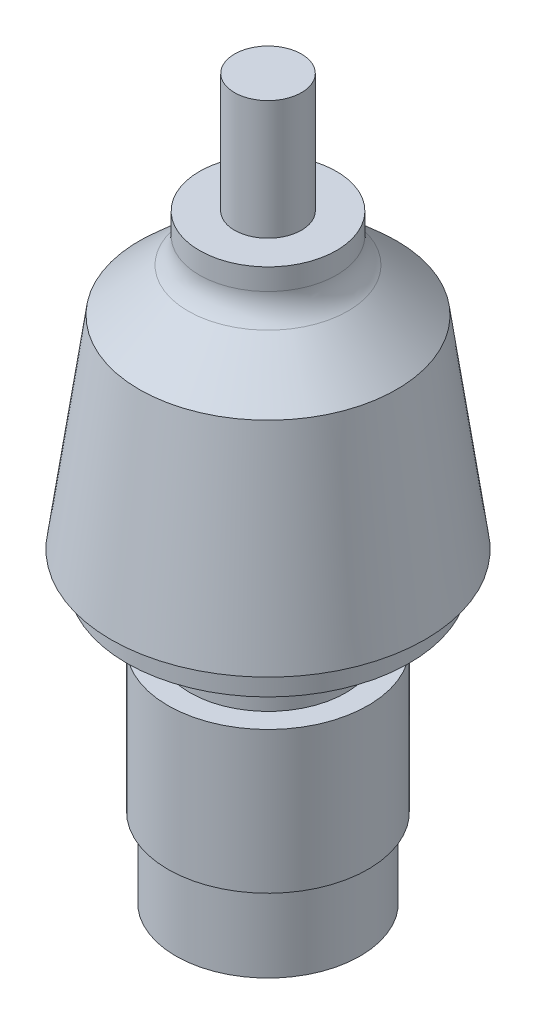
SolidWorks part; units mm, degrees
ref_plane "Front Plane" through (0, 0, 0) normal (0, 0, 1) x (1, 0, 0)
ref_plane "Top Plane" through (0, 0, 0) normal (0, 1, 0) x (1, 0, 0)
ref_plane "Right Plane" through (0, 0, 0) normal (1, 0, 0) x (0, 0, -1)
sketch "Sketch1" plane through (0, 0, 0) normal (0, 1, 0) x (1, 0, 0)
  circle A0 centre (0, 0) radius 13.7541
  dimension "D1" = 27.5082
extrude "Boss-Extrude1" add sketch "Sketch1" along normal blind 11.7856
sketch "Sketch2" plane through (0, 11.7856, 0) normal (0, 1, 0) x (1, 0, 0)
  circle A0 centre (0, 0) radius 14.9225
  dimension "D1" = 29.845
extrude "Boss-Extrude2" add sketch "Sketch2" along normal blind 21.1582
sketch "Sketch3" plane through (0, 32.9438, 0) normal (0, 1, 0) x (1, 0, 0)
  circle A0 centre (0, 0) radius 11.6205
  dimension "D1" = 23.241
extrude "Boss-Extrude3" add sketch "Sketch3" along normal blind 8.5598
sketch "Sketch4" plane through (0, 41.5036, 0) normal (0, 1, 0) x (1, 0, 0)
  circle A0 centre (0, 0) radius 21.082
  dimension "D1" = 42.164
extrude "Boss-Extrude4" add sketch "Sketch4" along normal blind 4.2164
sketch "Sketch5" plane through (0, 45.72, 0) normal (0, 1, 0) x (1, 0, 0)
  circle A0 centre (0, 0) radius 23.4315
  dimension "D1" = 46.863
ref_plane "Plane1" through (0, 75.9206, 0) normal (0, 1, 0) x (1, 0, 0)
sketch "Sketch6" plane through (0, 75.9206, 0) normal (0, 1, 0) x (1, 0, 0)
  circle A0 centre (0, 0) radius 19.2024
  dimension "D1" = 38.4048
loft "Loft1" add profiles "Sketch6", "Sketch5"
ref_plane "Plane2" through (0, 83.9216, 0) normal (0, 1, 0) x (1, 0, 0)
sketch "Sketch8" plane through (0, 83.9216, 0) normal (0, 1, 0) x (1, 0, 0)
  circle A0 centre (0, 0) radius 10.2235
  dimension "D1" = 20.447
loft "Loft2" add profiles "Sketch8" section edge at (0, 75.9206, 19.2024) section "Sketch8"
sketch "Sketch9" plane through (0, 83.9216, 0) normal (0, 1, 0) x (1, 0, 0)
  circle A0 centre (0, 0) radius 10.2235
extrude "Boss-Extrude5" add sketch "Sketch9" along normal blind 5.461
sketch "Sketch11" plane through (0, 89.3826, 0) normal (0, 1, 0) x (1, 0, 0)
  circle A0 centre (0, 0) radius 4.9911
  dimension "D1" = 9.9822
extrude "Boss-Extrude6" add sketch "Sketch11" along normal blind 17.78
fillet "Fillet1" radius 5.08 1 edges at (0, 83.9216, 10.2235)
